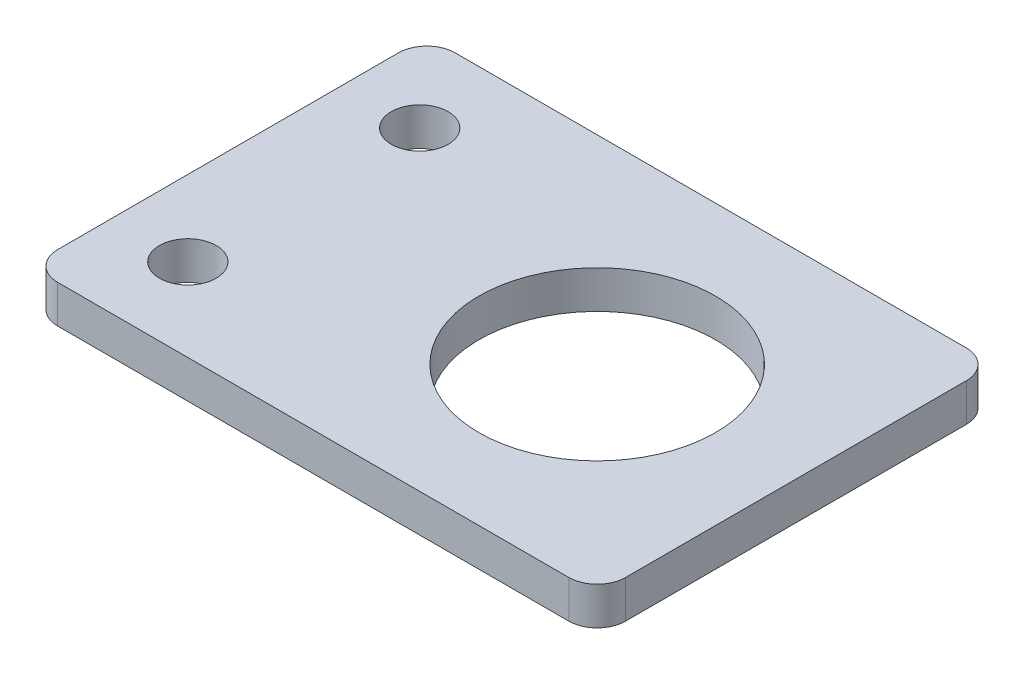
SolidWorks part; units mm, degrees
ref_plane "Front Plane" through (0, 0, 0) normal (0, 0, 1) x (1, 0, 0)
ref_plane "Top Plane" through (0, 0, 0) normal (0, 1, 0) x (1, 0, 0)
ref_plane "Right Plane" through (0, 0, 0) normal (1, 0, 0) x (0, 0, -1)
sketch "Sketch1" plane through (0, 0, 0) normal (0, 1, 0) x (1, 0, 0)
  line L0 (-30, 0) -> (30, 0) construction
  line L1 (-30, 21) -> (30, 21)
  line L2 (-30, 21) -> (-30, -21)
  line L3 (-30, -21) -> (30, -21)
  line L4 (30, 21) -> (30, -21)
  line L5 (-30, 21) -> (30, -21) construction
  line L6 (-30, -21) -> (30, 21) construction
  circle A0 centre (9, 0) radius 12.5
  circle A1 centre (-22, 12.25) radius 3
  circle A2 centre (-22, -12.25) radius 3
  point P0 (0, 0)
  dimension "D3" = 25
  dimension "D7" = 6
  dimension "D8" = 6
  dimension "D1" = 60
  dimension "D5" = 12.25
  dimension "D6" = 12.25
  dimension "D9" = 8
  dimension "D10" = 8
extrude "Boss-Extrude1" add sketch "Sketch1" along normal blind 4
fillet "Fillet2" radius 3 4 edges at (-30, 2, 21) (30, 2, 21) (-30, 2, -21) (30, 2, -21)
